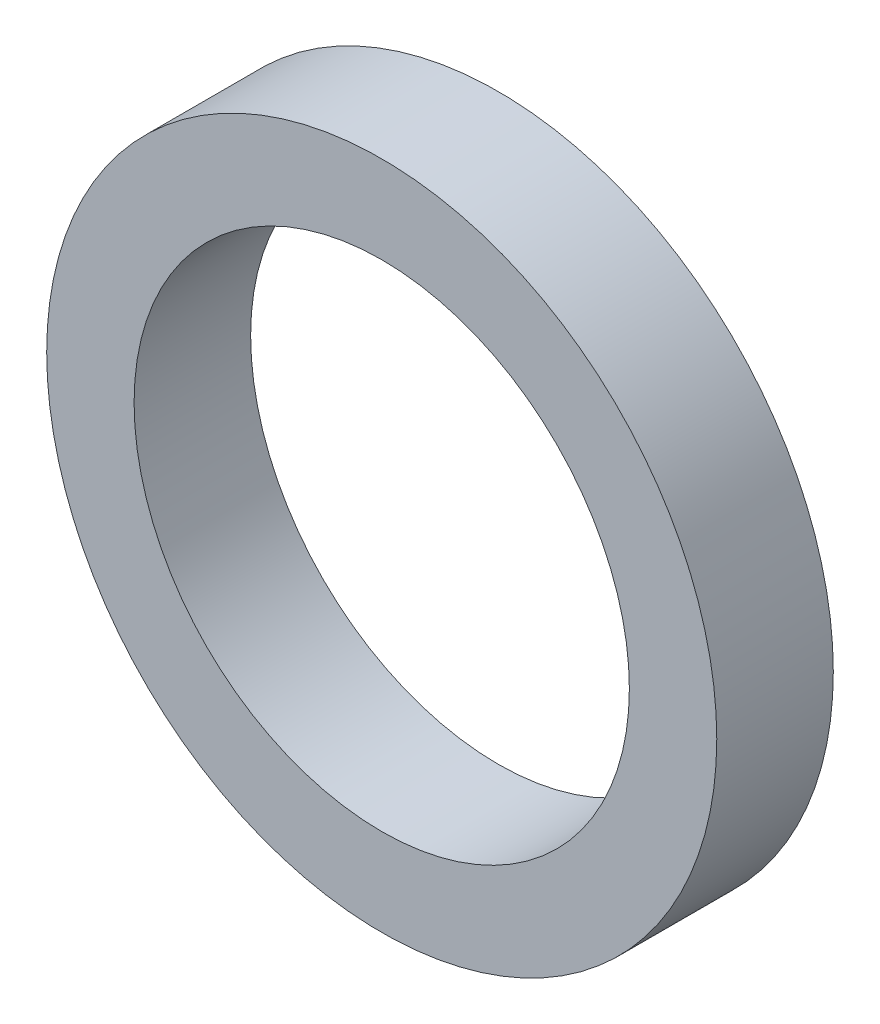
SolidWorks part; units mm, degrees
ref_plane "前视基准面" through (0, 0, 0) normal (0, 0, 1) x (1, 0, 0)
ref_plane "上视基准面" through (0, 0, 0) normal (0, 1, 0) x (1, 0, 0)
ref_plane "右视基准面" through (0, 0, 0) normal (1, 0, 0) x (0, 0, -1)
sketch "草图1" plane through (0, 0, 0) normal (0, 0, 1) x (1, 0, 0)
  circle A0 centre (0, 0) radius 8.5
  circle A1 centre (0, 0) radius 11.5
extrude "凸台-拉伸1" add sketch "草图1" along normal blind 4
